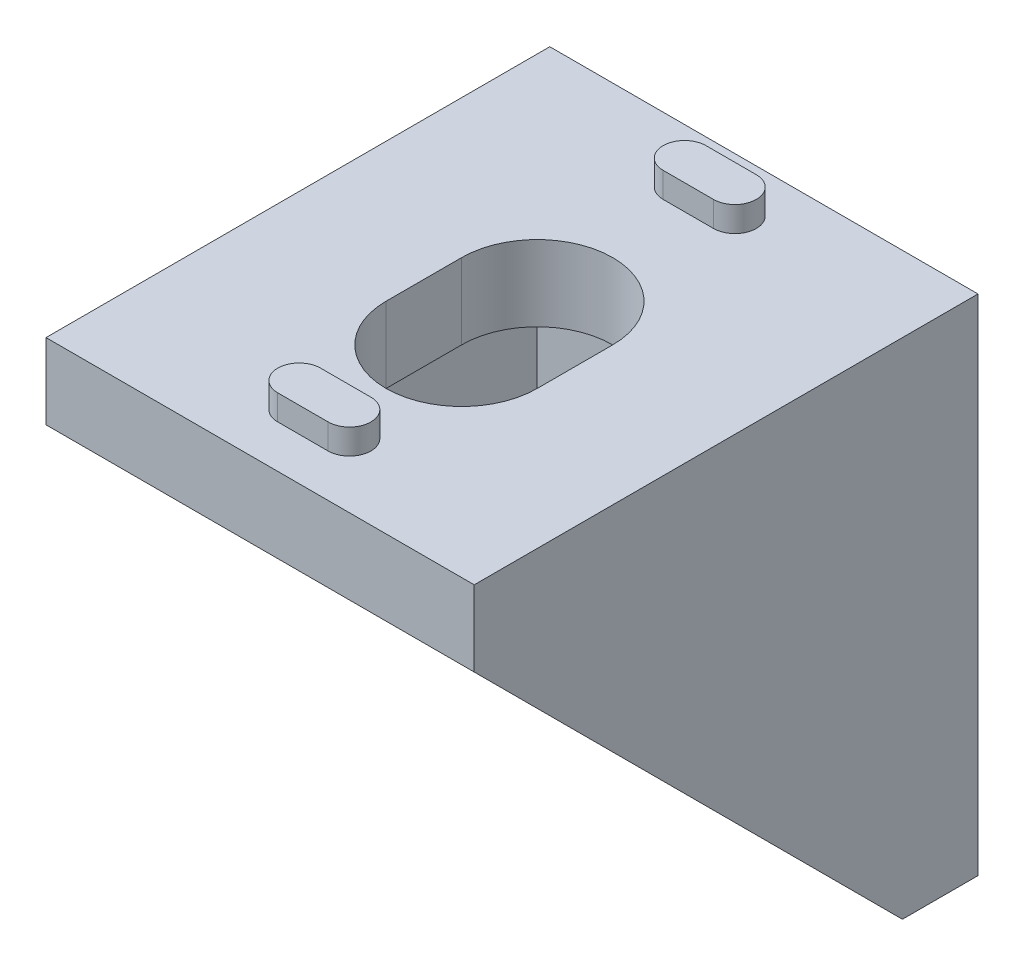
SolidWorks part; units mm, degrees
material "1060 Alloy"
ref_plane "Front Plane" through (0, 0, 0) normal (0, 0, 1) x (1, 0, 0)
ref_plane "Top Plane" through (0, 0, 0) normal (0, 1, 0) x (1, 0, 0)
ref_plane "Right Plane" through (0, 0, 0) normal (1, 0, 0) x (0, 0, -1)
sketch "Sketch1" plane through (0, 0, 0) normal (1, 0, 0) x (0, 0, -1)
  line L0 (0, 0) -> (-20, 0)
  line L1 (-20, 0) -> (-20, -3)
  line L2 (-20, -3) -> (-11.5, -11.5)
  line L3 (-11.5, -11.5) -> (0, 0) construction
  line L4 (-3, -20) -> (-11.5, -11.5)
  line L5 (0, -20) -> (-3, -20)
  line L6 (0, 0) -> (0, -20)
  point P7 (-26.4657, -3.9507)
  dimension "D1" = 3
  dimension "D2" = 20
extrude "Boss-Extrude1" add sketch "Sketch1" along normal mid plane 17
sketch "Sketch2" plane through (0, 0, 0) normal (1, 0, 0) x (0, 0, -1)
  line L0 (-20, -3) -> (-3, -20) construction
  line L1 (-3, -3) -> (-20, -3)
  line L2 (-3, -3) -> (-3, -20)
  line L3 (-3, -20) -> (-20, -20)
  line L4 (-20, -3) -> (-20, -20)
  line L5 (-20, 0) -> (-20, -3) construction
  point P4 (-20, -3)
  point P9 (-3, -20)
extrude "Cut-Extrude1" cut sketch "Sketch2" against normal mid plane 12
sketch "Sketch3" plane through (0, 0, 3) normal (0, 0, 1) x (1, 0, 0)
  line L0 (0, -9) -> (0, -12) construction
  line L1 (-3, -9) -> (-3, -12)
  line L2 (3, -9) -> (3, -12)
  line L3 (0, -10.5) -> (0.7454, -10.5) construction
  line L4 (-6, -20) -> (6, -20) construction
  arc A0 (-3, -9) -> (3, -9) centre (0, -9) cw
  arc A1 (-3, -12) -> (3, -12) centre (0, -12) ccw
  point P8 (0, -10.5)
  dimension "D3" = 9
  dimension "D4" = 5
  dimension "D1" = 3
  dimension "D2" = 3
extrude "Cut-Extrude2" cut sketch "Sketch3" against normal up to next (3 mm away)
sketch "Sketch4" plane through (0, 0, 0) normal (0, 0, -1) x (-1, 0, 0)
  line L0 (-1, -2.15) -> (1, -2.15) construction
  line L1 (-1, -3) -> (1, -3)
  line L2 (-1, -1.3) -> (1, -1.3)
  line L3 (0, 0) -> (0, -2.15) construction
  line L4 (-8.5, 0) -> (8.5, 0) construction
  line L5 (-2.1032, -9.8) -> (3, -9.8) construction
  line L6 (-1, -18.3) -> (1, -18.3)
  line L7 (-1, -16.6) -> (1, -16.6)
  line L8 (3, -12) -> (3, -9) construction
  arc A0 (-1, -3) -> (-1, -1.3) centre (-1, -2.15) cw
  arc A1 (1, -3) -> (1, -1.3) centre (1, -2.15) ccw
  arc A2 (1, -16.6) -> (1, -18.3) centre (1, -17.45) cw
  arc A3 (-1, -16.6) -> (-1, -18.3) centre (-1, -17.45) ccw
  point P14 (1, -16.6)
  point P17 (1, -18.3)
  point P21 (3, -9.8)
  dimension "D3" = 3.7
  dimension "D4" = 3
  dimension "D5" = 17
  dimension "D1" = 0.85
  dimension "D2" = 0.85
extrude "Boss-Extrude2" add sketch "Sketch4" along normal blind 1
ref_plane "Plane1" through (0, 0, 0) normal (0, 0.7071, 0.7071) x (-1, 0, 0)
mirror "Mirror1" about plane through (0, 0, 0) normal (0, 0.7071, 0.7071) of "Boss-Extrude2", "Cut-Extrude2"
